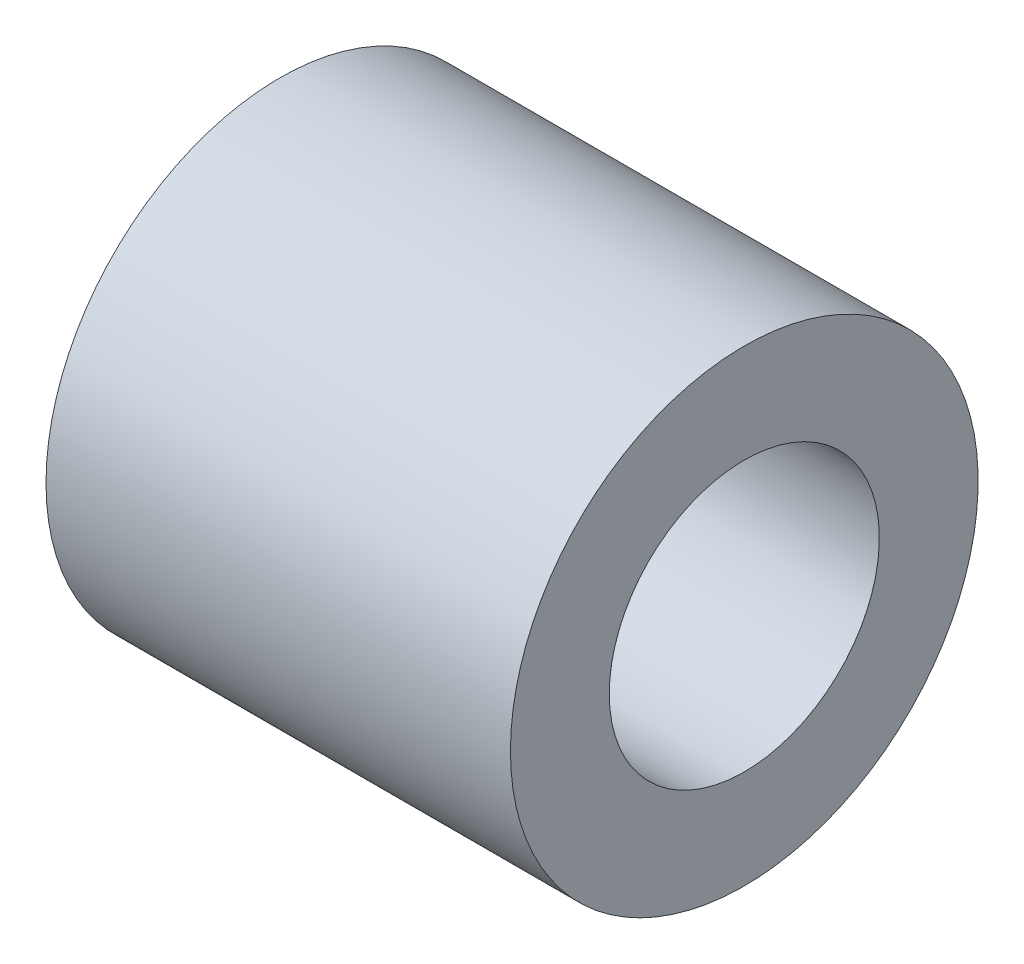
SolidWorks part; units mm, degrees
material "ABS"
ref_plane "Front Plane" through (0, 0, 0) normal (0, 0, 1) x (1, 0, 0)
ref_plane "Top Plane" through (0, 0, 0) normal (0, 1, 0) x (1, 0, 0)
ref_plane "Right Plane" through (0, 0, 0) normal (1, 0, 0) x (0, 0, -1)
sketch "Sketch1" plane through (0, 0, 0) normal (0, 1, 0) x (1, 0, 0)
  line L0 (0, 0) -> (22.4144, 0) construction
  line L1 (0, 0) -> (14.1, 0)
  line L2 (0, 0) -> (0, -4.1)
  line L3 (0, -4.1) -> (14.1, -4.1)
  line L4 (14.1, 0) -> (14.1, -4.1)
  line L5 (0, 0) -> (14.1, 0)
  line L6 (0, 0) -> (0, -7.1)
  line L7 (0, -7.1) -> (14.1, -7.1)
  line L8 (14.1, 0) -> (14.1, -7.1)
  dimension "D1" = 14.1
  dimension "D2" = 4.1
  dimension "D3" = 3
revolve "Revolve1" add sketch "Sketch1" angle 360 about L0
